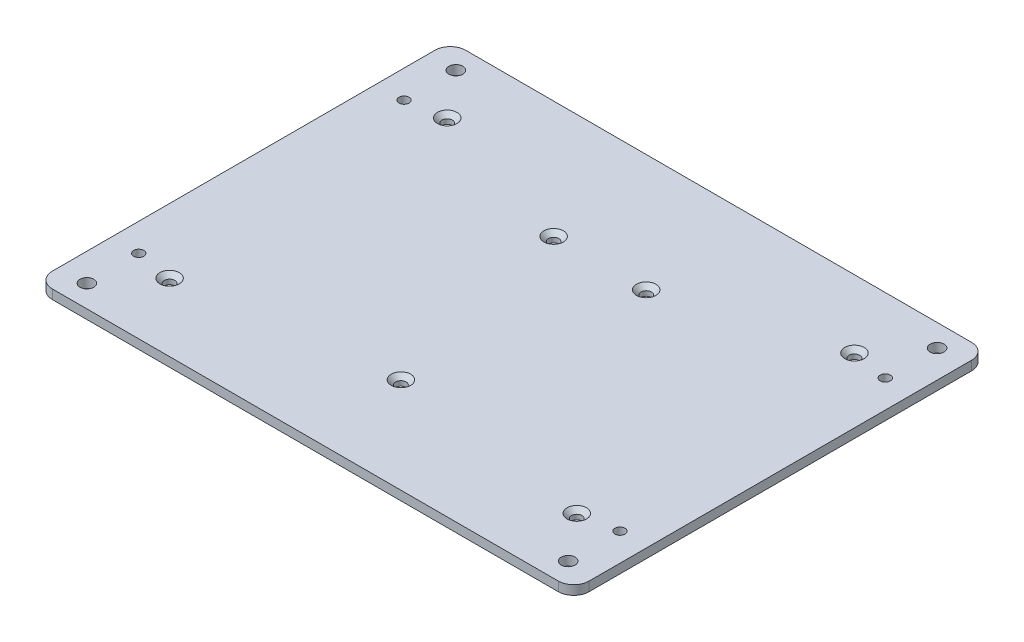
SolidWorks part; units mm, degrees
material "1060 Alloy"
ref_plane "Front Plane" through (0, 0, 0) normal (0, 0, 1) x (1, 0, 0)
ref_plane "Top Plane" through (0, 0, 0) normal (0, 1, 0) x (1, 0, 0)
ref_plane "Right Plane" through (0, 0, 0) normal (1, 0, 0) x (0, 0, -1)
sketch "Sketch1" plane through (0, 0, 0) normal (0, 1, 0) x (1, 0, 0)
  line L1 (87, 67) -> (-87, 67)
  line L2 (87, 67) -> (87, -67)
  line L3 (87, -67) -> (-87, -67)
  line L4 (-87, 67) -> (-87, -67)
  line L5 (87, 67) -> (-87, -67) construction
  line L6 (87, -67) -> (-87, 67) construction
  point P0 (0, 0)
  dimension "D1" = 134
  dimension "D2" = 174
extrude "Boss-Extrude1" add sketch "Sketch1" along normal blind 3
hole_wizard "Assem71" positions "Sketch2" profile "Sketch4" tap size "M4" standard "DIN" end condition through all
sketch "Sketch2" plane through (0, 3, 0) normal (0, 1, 0) x (1, 0, 0)
  line L0 (-77.9991, 42.9991) -> (-77.9991, 59.7991) construction
  line L2 (-77.9991, -42.9991) -> (-77.9991, -59.7991) construction
  line L4 (77.9991, -42.9991) -> (-77.9991, -42.9991) construction
  line L5 (77.9991, -42.9991) -> (77.9991, 42.9991) construction
  line L6 (77.9991, 42.9991) -> (-77.9991, 42.9991) construction
  line L7 (-77.9991, -42.9991) -> (-77.9991, 42.9991) construction
  line L8 (77.9991, -42.9991) -> (-77.9991, 42.9991) construction
  line L9 (77.9991, 42.9991) -> (-77.9991, -42.9991) construction
  line L10 (77.9991, 42.9991) -> (77.9991, 59.7991) construction
  line L12 (77.9991, -42.9991) -> (77.9991, -59.7991) construction
  point P0 (-77.9991, 42.9991)
  point P3 (77.9991, 42.9991)
  point P6 (77.9991, -42.9991)
  point P9 (-77.9991, -42.9991)
  point P11 (-77.9991, 59.7991)
  point P13 (-77.9991, -59.7991)
  point P153 (77.9991, 59.7991)
  point P161 (77.9991, -59.7991)
  dimension "D1" = 16.8
sketch "Sketch4" plane through (-77.9991, 3, -42.9991) normal (1, 0, 0) x (0, 0, 1)
  line L0 (0, 0) -> (0, 3)
  line L1 (0, 3) -> (1.65, 3)
  line L2 (1.65, 3) -> (1.65, 0)
  line L5 (1.65, 0) -> (0, 0)
  line L11 (0, -6.35) -> (0, 107.95) construction
  dimension "Thru Tap Drill Dia." = 3.3
  dimension "Thru Tap Drill Depth" = 3
cosmetic thread "Hole Thread1"
cosmetic thread "Hole Thread2"
cosmetic thread "Hole Thread3"
cosmetic thread "Hole Thread4"
cosmetic thread "Hole Thread17"
cosmetic thread "Hole Thread18"
cosmetic thread "Hole Thread19"
cosmetic thread "Hole Thread20"
fillet "Fillet1" radius 5 4 edges at (87, 1.5, -67) (87, 1.5, 67) (-87, 1.5, 67) (-87, 1.5, -67)
hole_wizard "CSK for M3 Countersunk Flat Head Screw1" positions "Sketch5" profile "Sketch6" countersink size "M3" standard "ISO" end condition through all
sketch "Sketch5" plane through (0, 3, 0) normal (0, 1, 0) x (1, 0, 0)
  point P0 (-66, 45)
  point P3 (66, 45)
  point P9 (-66, -45)
  point P18 (66, -45)
sketch "Sketch6" plane through (-66, 3, -45) normal (1, 0, 0) x (0, 0, 1)
  line L0 (0, 0) -> (0, 3)
  line L1 (0, 3) -> (1.7, 3)
  line L2 (1.7, 3) -> (1.7, 1.45)
  line L3 (1.7, 1.45) -> (3.15, 0)
  line L5 (3.15, 0) -> (0, 0)
  line L6 (-1.7, 1.45) -> (-3.15, 0) construction
  line L11 (0, -6.35) -> (0, 107.95) construction
  dimension "Thru Hole Dia." = 3.4
  dimension "Thru Hole Depth" = 3
  dimension "Near C'Sink Dia." = 6.3
  dimension "Near C'Sink Angle" = 90
hole_wizard "CSK for M3 Countersunk Flat Head Screw2" positions "Sketch7" profile "Sketch8" countersink size "M3" standard "DIN" end condition through all
sketch "Sketch7" plane through (0, 3, 0) normal (0, 1, 0) x (1, 0, 0)
  circle A3 centre (0, -36) radius 1.7
  circle A4 centre (14.5, 29) radius 1.7
  circle A5 centre (-15.5, 29) radius 1.7
  point P1 (0, -36)
  point P3 (14.5, 29)
  point P5 (-15.5, 29)
sketch "Sketch8" plane through (0, 3, 36) normal (1, 0, 0) x (0, 0, 1)
  line L0 (0, 0) -> (0, 3)
  line L1 (0, 3) -> (1.7, 3)
  line L2 (1.7, 3) -> (1.7, 1.45)
  line L3 (1.7, 1.45) -> (3.15, 0)
  line L5 (3.15, 0) -> (0, 0)
  line L6 (-1.7, 1.45) -> (-3.15, 0) construction
  line L11 (0, -6.35) -> (0, 107.95) construction
  dimension "Thru Hole Dia." = 3.4
  dimension "Thru Hole Depth" = 3
  dimension "Near C'Sink Dia." = 6.3
  dimension "Near C'Sink Angle" = 90
sketch "Sketch9" plane through (0, 0, 0) normal (0, -1, 0) x (1, 0, 0)
  circle A0 centre (-77.9991, 59.7991) radius 5.5 construction
  circle A1 centre (77.9991, 59.7991) radius 5.5 construction
  circle A2 centre (-77.9991, -59.7991) radius 5.5 construction
  circle A3 centre (77.9991, -59.7991) radius 5.5 construction
  point P0 (-77.9991, -59.7991)
  point P2 (77.9991, -59.7991)
  point P4 (77.9991, 59.7991)
  point P6 (-77.9991, 59.7991)
hole_wizard "M4 Clearance Hole1" positions "Sketch9" profile "Sketch10" hole size "M4" standard "DIN" end condition through all
sketch "Sketch10" plane through (-77.9991, 0, -59.7991) normal (1, 0, 0) x (0, 0, -1)
  line L0 (0, 0) -> (0, 3)
  line L1 (0, 3) -> (2.25, 3)
  line L2 (2.25, 3) -> (2.25, 0)
  line L5 (2.25, 0) -> (0, 0)
  line L11 (0, -6.35) -> (0, 107.95) construction
  dimension "Thru Hole Dia." = 4.5
  dimension "Thru Hole Depth" = 3
